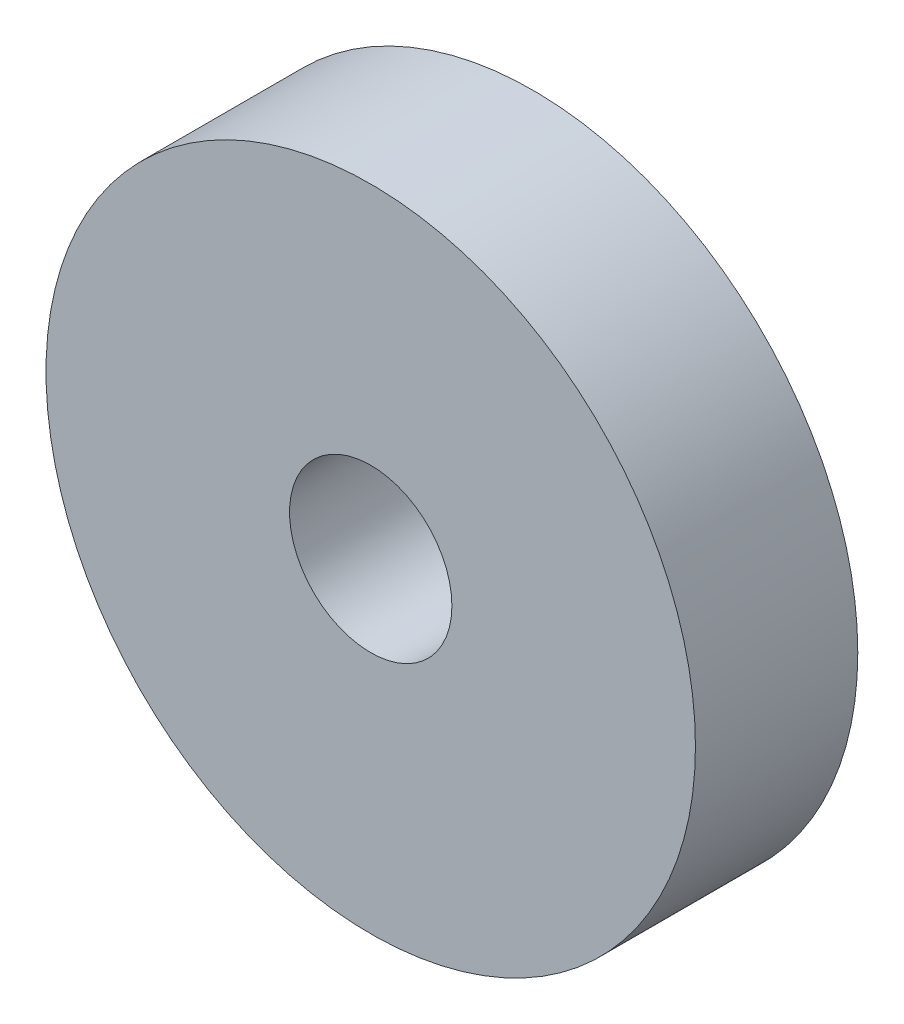
SolidWorks part; units mm, degrees
ref_plane "Front Plane" through (0, 0, 0) normal (0, 0, 1) x (1, 0, 0)
ref_plane "Top Plane" through (0, 0, 0) normal (0, 1, 0) x (1, 0, 0)
ref_plane "Right Plane" through (0, 0, 0) normal (1, 0, 0) x (0, 0, -1)
sketch "Sketch1" plane through (0, 0, 0) normal (0, 0, 1) x (1, 0, 0)
  circle A0 centre (0, 0) radius 10
  circle A1 centre (0, 0) radius 2.5
  dimension "D1" = 20
  dimension "D2" = 5
extrude "Boss-Extrude1" add sketch "Sketch1" along normal blind 5
